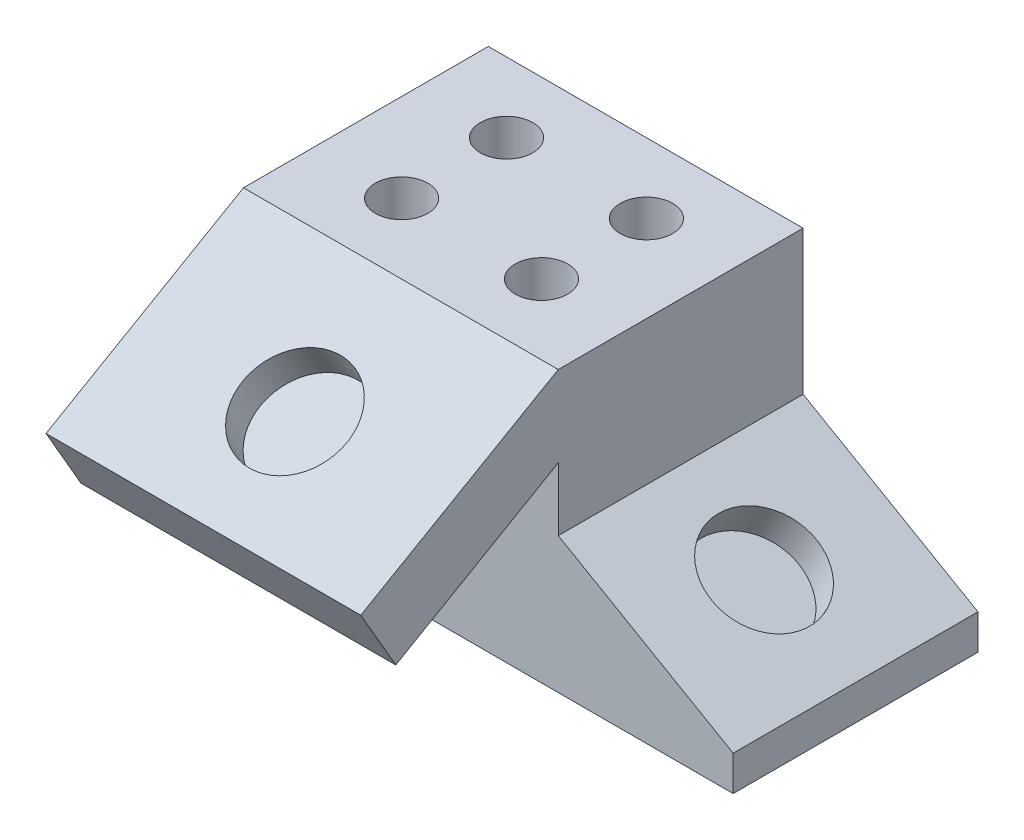
SolidWorks part; units mm, degrees
ref_plane "Front Plane" through (0, 0, 0) normal (0, 0, 1) x (1, 0, 0)
ref_plane "Top Plane" through (0, 0, 0) normal (0, 1, 0) x (1, 0, 0)
ref_plane "Right Plane" through (0, 0, 0) normal (1, 0, 0) x (0, 0, -1)
sketch "Sketch1" plane through (0, 0, 0) normal (0, 0, 1) x (1, 0, 0)
  line L0 (57.15, 0) -> (88.9, 0)
  line L1 (0, 0) -> (57.15, 0)
  line L2 (0, 0) -> (0, 50.8)
  line L3 (0, 50.8) -> (57.15, 50.8)
  line L4 (57.15, 24.6809) -> (57.15, 50.8)
  line L5 (88.9, 0) -> (88.9, 6.35)
  line L6 (88.9, 6.35) -> (57.15, 24.6809)
  dimension "D1" = 6.35
  dimension "D2" = 57.15
  dimension "D3" = 31.75
  dimension "D4" = 60
  dimension "D5" = 50.8
  dimension "D6" = 26.1191
extrude "Boss-Extrude1" add sketch "Sketch1" against normal blind 44.45
sketch "Sketch2" plane through (0, 50.8, 0) normal (0, 1, 0) x (1, 0, 0)
  line L0 (0, 44.45) -> (0, 0) construction
  line L1 (57.15, 0) -> (0, 0) construction
  line L2 (16.002, 12.7) -> (41.402, 12.7) construction
  line L3 (16.002, 12.7) -> (16.002, 31.75) construction
  circle A0 centre (16.002, 12.7) radius 4.7625
  circle A1 centre (41.402, 12.7) radius 4.7625
  circle A2 centre (41.402, 31.75) radius 4.7625
  circle A3 centre (16.002, 31.75) radius 4.7625
  dimension "D1" = 9.525
  dimension "D2" = 16.002
  dimension "D3" = 12.7
  dimension "D6" = 90
  dimension "D4" = 2
  dimension "D5" = 2
extrude "Cut-Extrude1" cut sketch "Sketch2" against normal blind 12.7
sketch "Sketch3" plane through (24.9746, 43.2573, 0) normal (0.5, 0.866, 0) x (0.866, -0.5, 0)
  line L0 (73.8147, 44.45) -> (37.1529, 44.45) construction
  line L1 (73.8147, 44.45) -> (73.8147, 0) construction
  circle A0 centre (54.7647, 22.098) radius 9.525
  dimension "D1" = 19.05
  dimension "D2" = 22.352
  dimension "D3" = 19.05
extrude "Cut-Extrude2" cut sketch "Sketch3" against normal blind 6.35
sketch "Sketch4" plane through (57.15, 0, 0) normal (1, 0, 0) x (0, 0, -1)
  line L0 (0, 50.8) -> (-35.8552, 30.099)
  line L1 (-35.8552, 30.099) -> (-29.5052, 19.1005)
  line L2 (-29.5052, 19.1005) -> (0, 36.1353)
  line L3 (0, 24.6809) -> (0, 50.8) construction
  line L4 (44.45, 50.8) -> (0, 50.8) construction
  line L9 (0, 50.8) -> (0, 24.6809)
  line L10 (0, 24.6809) -> (44.45, 24.6809)
  line L11 (44.45, 24.6809) -> (44.45, 50.8)
  line L12 (44.45, 50.8) -> (0, 50.8)
  line L13 (0, 50.8) -> (0, 36.1353)
  dimension "D1" = 41.402
  dimension "D2" = 30
  dimension "D3" = 12.7
  dimension "D4" = 0
extrude "Boss-Extrude2" add sketch "Sketch4" against normal blind 57.15
sketch "Sketch5" plane through (0, 38.1, 21.997) normal (0, 0.866, 0.5) x (1, 0, 0)
  line L0 (0, 25.4) -> (0, -16.002) construction
  line L1 (57.15, 25.4) -> (0, 25.4) construction
  circle A0 centre (28.702, 3.048) radius 9.525
  dimension "D1" = 19.05
  dimension "D2" = 28.702
  dimension "D3" = 22.352
extrude "Cut-Extrude3" cut sketch "Sketch5" against normal blind 6.35
